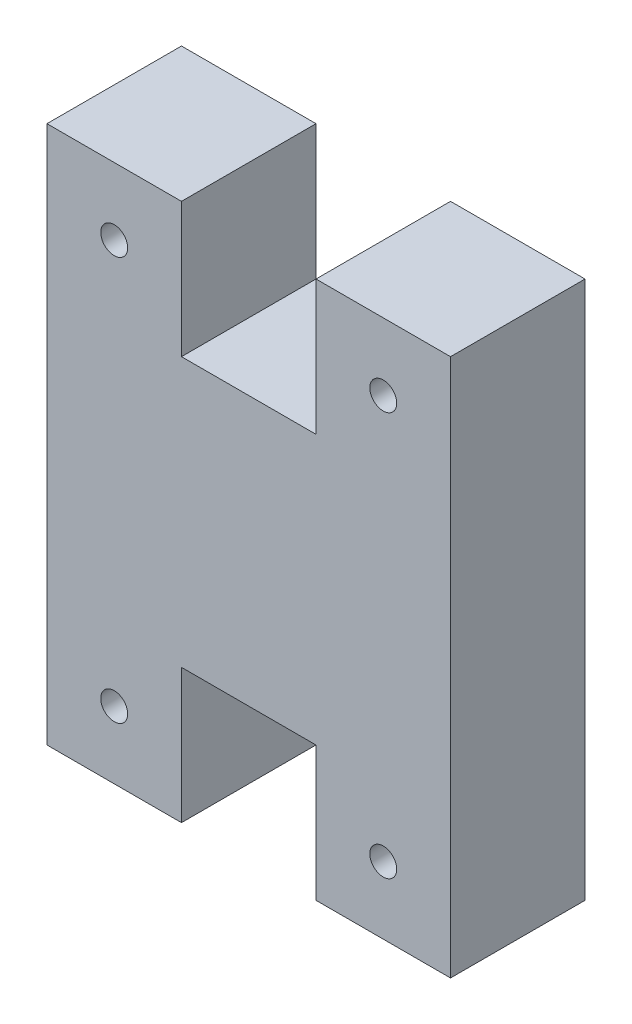
SolidWorks part; units mm, degrees
ref_plane "Front Plane" through (0, 0, 0) normal (0, 0, 1) x (1, 0, 0)
ref_plane "Top Plane" through (0, 0, 0) normal (0, 1, 0) x (1, 0, 0)
ref_plane "Right Plane" through (0, 0, 0) normal (1, 0, 0) x (0, 0, -1)
sketch "Sketch1" plane through (0, 0, 0) normal (0, 0, 1) x (1, 0, 0)
  line L1 (0, 0) -> (19.05, 0)
  line L2 (0, 0) -> (0, 25.4)
  line L3 (0, 25.4) -> (19.05, 25.4)
  line L4 (19.05, 0) -> (19.05, 25.4)
  dimension "D1" = 19.05
  dimension "D2" = 25.4
extrude "Boss-Extrude1" add sketch "Sketch1" along normal blind 6.35
sketch "Sketch2" plane through (0, 0, 6.35) normal (0, 0, 1) x (1, 0, 0)
  line L0 (6.35, 25.4) -> (6.35, 19.05)
  line L1 (19.05, 25.4) -> (0, 25.4) construction
  line L2 (12.7, 25.4) -> (12.7, 19.05)
  line L3 (6.35, 19.05) -> (12.7, 19.05)
  line L4 (6.35, 19.05) -> (0, 19.05) construction
  line L7 (0, 25.4) -> (0, 0) construction
  line L8 (6.35, 25.4) -> (12.7, 25.4)
  dimension "D1" = 6.35
  dimension "D2" = 6.35
  dimension "D3" = 6.35
extrude "Cut-Extrude1" cut sketch "Sketch2" against normal through all
ref_plane "Plane1" through (0, 12.7, 0) normal (0, 1, 0) x (1, 0, 0)
mirror "Mirror1" about plane through (0, 12.7, 0) normal (0, 1, 0) of "Cut-Extrude1"
sketch "Sketch6" plane through (0, 0, 6.35) normal (0, 0, 1) x (1, 0, 0)
  line L0 (6.35, 25.4) -> (0, 25.4) construction
  line L1 (0, 25.4) -> (0, 19.05) construction
  line L2 (0, 19.05) -> (6.35, 19.05) construction
  line L3 (6.35, 19.05) -> (6.35, 25.4) construction
  line L4 (19.05, 25.4) -> (12.7, 25.4) construction
  line L5 (12.7, 25.4) -> (12.7, 19.05) construction
  line L6 (12.7, 19.05) -> (19.05, 19.05) construction
  line L7 (19.05, 19.05) -> (19.05, 25.4) construction
  line L8 (6.35, 25.4) -> (0, 25.4) construction
  line L9 (0, 25.4) -> (0, 19.05) construction
  line L10 (0, 19.05) -> (6.35, 19.05) construction
  line L11 (6.35, 19.05) -> (6.35, 25.4) construction
  line L12 (19.05, 25.4) -> (12.7, 25.4) construction
  line L13 (12.7, 25.4) -> (12.7, 19.05) construction
  line L14 (12.7, 19.05) -> (19.05, 19.05) construction
  line L15 (19.05, 19.05) -> (19.05, 25.4) construction
  line L16 (3.175, 22.225) -> (0, 22.225) construction
  line L17 (3.175, 22.225) -> (3.175, 19.05) construction
  line L18 (15.875, 22.225) -> (19.05, 22.225) construction
  line L19 (15.875, 22.225) -> (15.875, 19.05) construction
  circle A0 centre (3.175, 22.225) radius 0.635
  circle A1 centre (15.875, 22.225) radius 0.635
  dimension "D1" = 1.27
extrude "Cut-Extrude2" cut sketch "Sketch6" against normal through all
sketch "Sketch7" plane through (0, 0, 0) normal (0, 0, -1) x (-1, 0, 0)
  line L0 (0, 6.35) -> (-6.35, 6.35) construction
  line L1 (-6.35, 6.35) -> (-6.35, 0) construction
  line L2 (-6.35, 0) -> (0, 0) construction
  line L3 (0, 0) -> (0, 6.35) construction
  line L4 (-12.7, 6.35) -> (-19.05, 6.35) construction
  line L5 (-19.05, 6.35) -> (-19.05, 0) construction
  line L6 (-19.05, 0) -> (-12.7, 0) construction
  line L7 (-12.7, 0) -> (-12.7, 6.35) construction
  line L8 (0, 6.35) -> (-6.35, 6.35) construction
  line L9 (-6.35, 6.35) -> (-6.35, 0) construction
  line L10 (-6.35, 0) -> (0, 0) construction
  line L11 (0, 0) -> (0, 6.35) construction
  line L12 (-12.7, 6.35) -> (-19.05, 6.35) construction
  line L13 (-19.05, 6.35) -> (-19.05, 0) construction
  line L14 (-19.05, 0) -> (-12.7, 0) construction
  line L15 (-12.7, 0) -> (-12.7, 6.35) construction
  line L16 (-15.875, 3.175) -> (-19.05, 3.175) construction
  line L17 (-15.875, 3.175) -> (-15.875, 0) construction
  line L18 (-3.175, 3.175) -> (0, 3.175) construction
  line L19 (-3.175, 3.175) -> (-3.175, 0) construction
  circle A0 centre (-15.875, 3.175) radius 0.635
  circle A1 centre (-3.175, 3.175) radius 0.635
  dimension "D1" = 1.27
extrude "Cut-Extrude3" cut sketch "Sketch7" against normal through all
